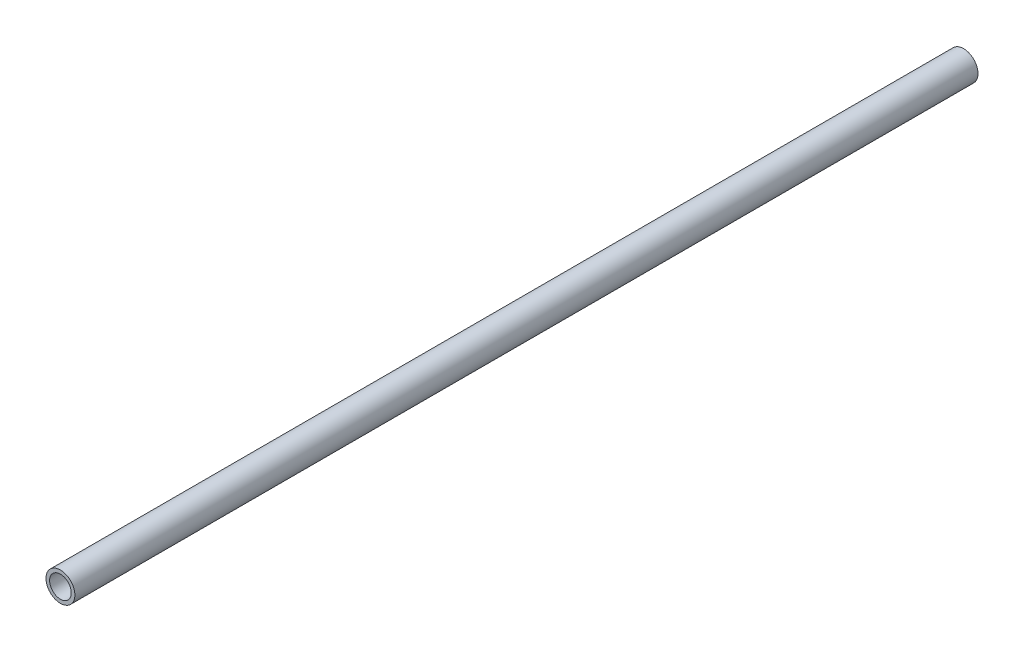
SolidWorks part; units mm, degrees
ref_plane "前视基准面" through (0, 0, 0) normal (0, 0, 1) x (1, 0, 0)
ref_plane "上视基准面" through (0, 0, 0) normal (0, 1, 0) x (1, 0, 0)
ref_plane "右视基准面" through (0, 0, 0) normal (1, 0, 0) x (0, 0, -1)
sketch "草图1" plane through (0, 0, 0) normal (0, 0, 1) x (1, 0, 0)
  circle A0 centre (0, 0) radius 3
  circle A1 centre (0, 0) radius 4
  dimension "D1" = 6
  dimension "D2" = 8
extrude "凸台-拉伸1" add sketch "草图1" along normal blind 250
